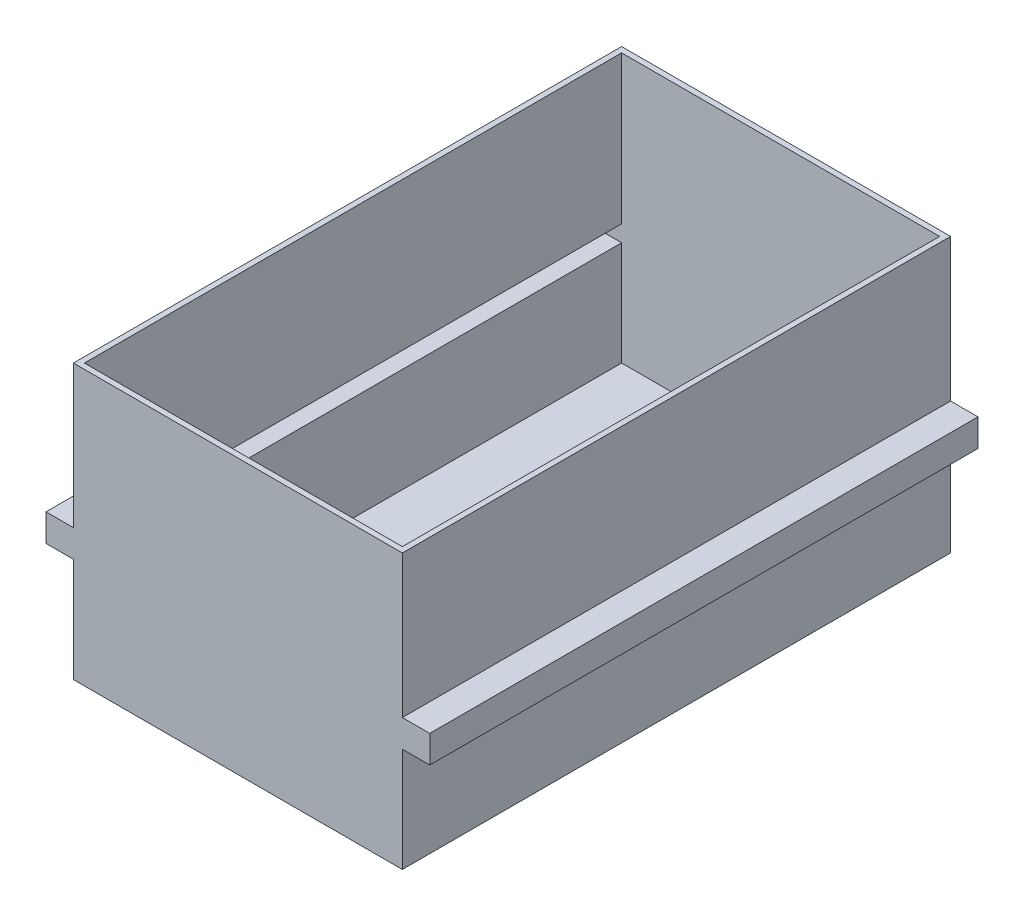
SolidWorks part; units mm, degrees
ref_plane "Alzado" through (0, 0, 0) normal (0, 0, 1) x (1, 0, 0)
ref_plane "Planta" through (0, 0, 0) normal (0, 1, 0) x (1, 0, 0)
ref_plane "Vista lateral" through (0, 0, 0) normal (1, 0, 0) x (0, 0, -1)
sketch "Croquis1" plane through (0, 0, 0) normal (0, 0, 1) x (1, 0, 0)
  line L1 (150, -125) -> (-150, -125)
  line L2 (150, -125) -> (150, 125)
  line L3 (150, 125) -> (-150, 125)
  line L4 (-150, -125) -> (-150, 125)
  line L5 (150, -125) -> (-150, 125) construction
  line L6 (150, 125) -> (-150, -125) construction
  point P0 (0, 0)
  dimension "D1" = 250
  dimension "D2" = 300
extrude "Saliente-Extruir1" add sketch "Croquis1" along normal blind 500
sketch "Croquis3" plane through (150, 0, 0) normal (1, 0, 0) x (0, 0, -1)
  line L7 (-500, -125) -> (-500, 125) construction
  line L8 (-500, -5) -> (0, -5)
  line L9 (-500, -5) -> (-500, -30)
  line L10 (-500, -30) -> (0, -30)
  line L11 (0, -5) -> (0, -30)
  line L12 (0, -125) -> (0, 125) construction
  line L13 (-500, 125) -> (0, 125) construction
  dimension "D1" = 25
  dimension "D2" = 130
extrude "Saliente-Extruir2" add sketch "Croquis3" along normal blind 25 and the other way blind 325
shell "Vaciado1" thickness 5
sketch "Croquis4" plane through (0, 0, 500) normal (0, 0, 1) x (1, 0, 0)
  line L7 (-150, 125) -> (-150, -5) construction
  line L8 (-150, 85) -> (150, 85)
  line L9 (-150, 85) -> (-150, 60)
  line L10 (-150, 60) -> (150, 60)
  line L11 (150, 85) -> (150, 60)
  line L12 (150, -5) -> (150, 125) construction
  line L13 (150, 125) -> (-150, 125) construction
  dimension "D1" = 25
  dimension "D2" = 40
extrude "Saliente-Extruir3" [suppressed] add sketch "Croquis4" along normal blind 60
sketch "Croquis5" [suppressed] plane through (0, 85, 0) normal (0, 1, 0) x (1, 0, 0)
  line L0 (-135, -515) -> (-135, -545)
  line L1 (-150, -500) -> (150, -500)
  line L2 (-150, -500) -> (-150, -560)
  line L3 (-150, -560) -> (150, -560)
  line L4 (150, -500) -> (150, -560)
  line L5 (-135, -545) -> (135, -545)
  line L6 (135, -515) -> (135, -545)
  line L8 (135, -515) -> (135, -500)
  line L9 (-135, -515) -> (-135, -500)
  line L11 (-135, -515) -> (135, -515) construction
  dimension "D1" = 15
extrude "Cortar-Extruir1" [suppressed] cut sketch "Croquis5" against normal blind 40 contours L11 L0 L5 L6 | L9 L11 L8 L1
